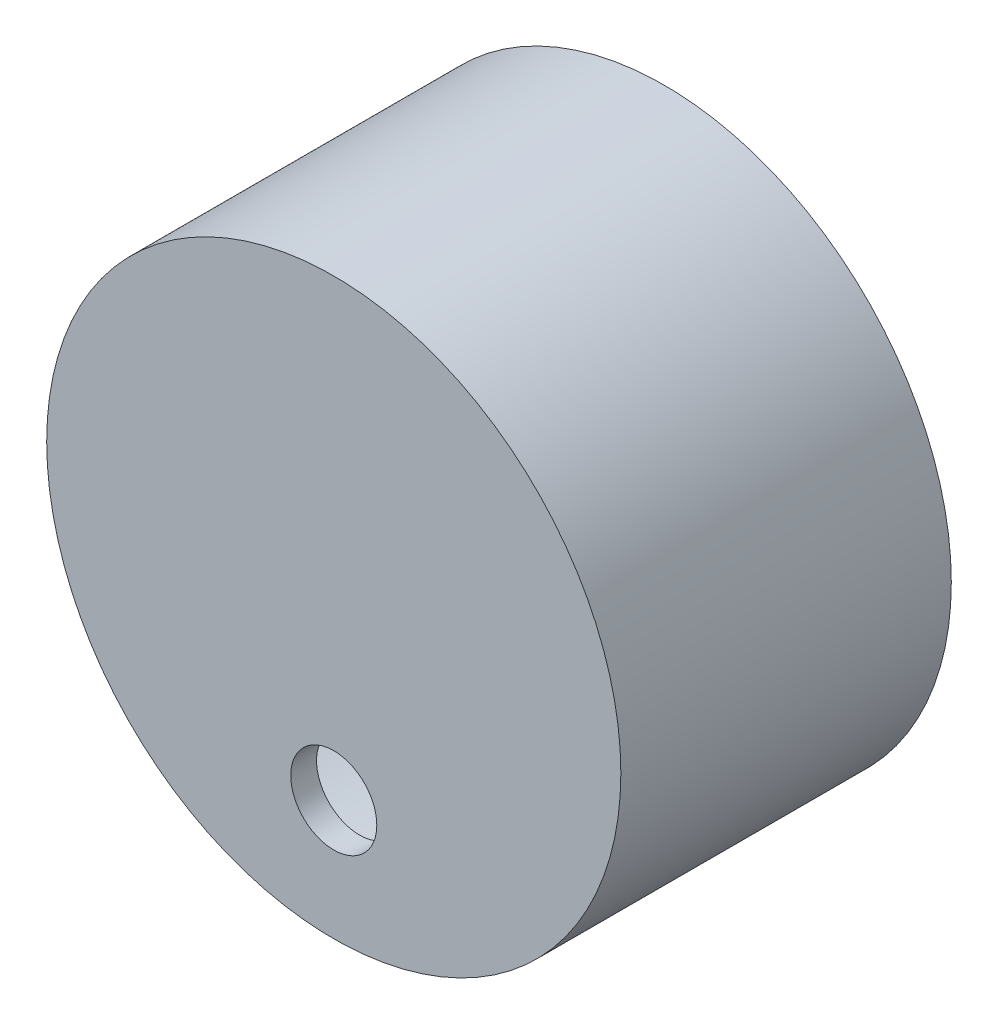
SolidWorks part; units mm, degrees
ref_plane "Front Plane" through (0, 0, 0) normal (0, 0, 1) x (1, 0, 0)
ref_plane "Top Plane" through (0, 0, 0) normal (0, 1, 0) x (1, 0, 0)
ref_plane "Right Plane" through (0, 0, 0) normal (1, 0, 0) x (0, 0, -1)
sketch "Sketch1" plane through (0, 0, 0) normal (0, 0, 1) x (1, 0, 0)
  circle A0 centre (22.75, 10.5) radius 30.3584
  circle A1 centre (22.75, 10.5) radius 33.3584
  dimension "D1" = 3
extrude "Boss-Extrude1" add sketch "Sketch1" along normal blind 25.4 and the other way up to surface (10 mm away)
sketch "Sketch2" plane through (0, 0, 25.4) normal (0, 0, 1) x (1, 0, 0)
  circle A0 centre (22.75, 10.5) radius 33.3584
  circle A1 centre (22.75, -8.9136) radius 5
extrude "Boss-Extrude2" add sketch "Sketch2" along normal blind 3
